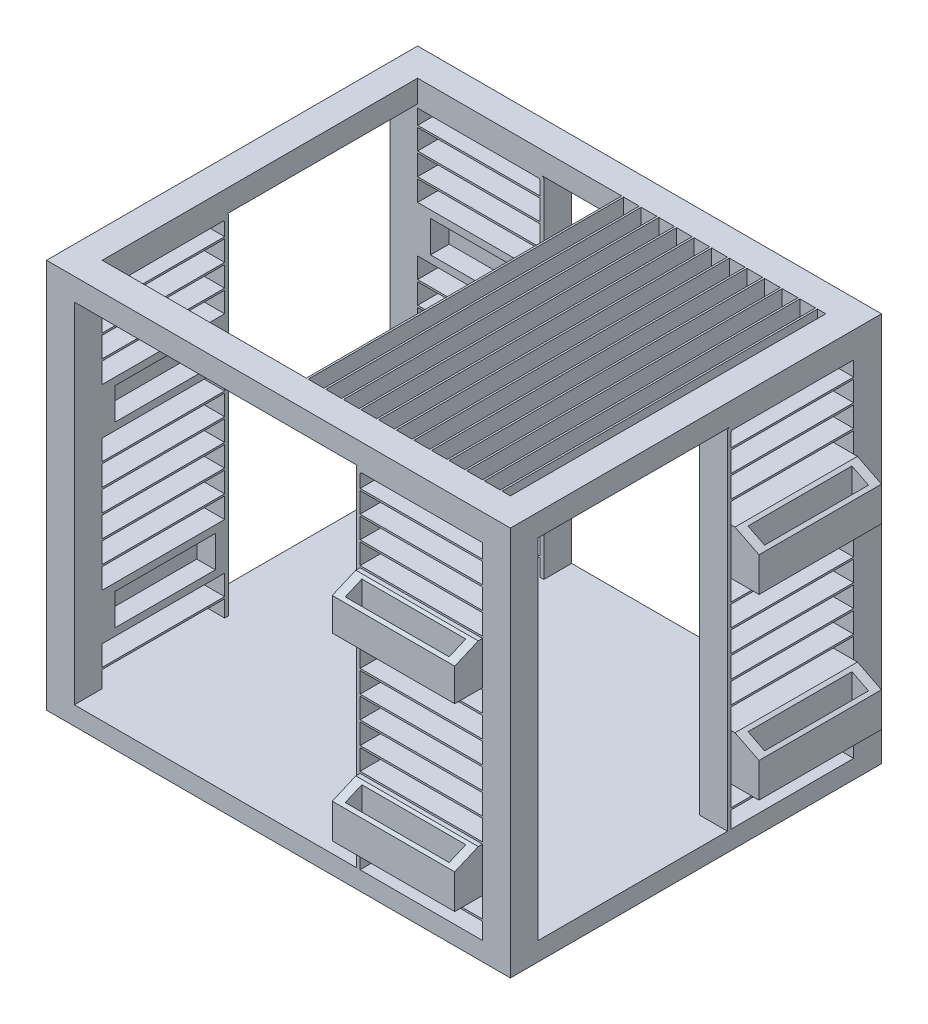
SolidWorks part; units mm, degrees
ref_plane "Front Plane" through (0, 0, 0) normal (0, 0, 1) x (1, 0, 0)
ref_plane "Top Plane" through (0, 0, 0) normal (0, 1, 0) x (1, 0, 0)
ref_plane "Right Plane" through (0, 0, 0) normal (1, 0, 0) x (0, 0, -1)
sketch "Sketch2" plane through (0, 0, 0) normal (0, 1, 0) x (1, 0, 0)
  line L1 (-1250, -1000) -> (1250, -1000)
  line L2 (-1250, -1000) -> (-1250, 1000)
  line L3 (-1250, 1000) -> (1250, 1000)
  line L4 (1250, -1000) -> (1250, 1000)
  line L5 (-1250, -1000) -> (1250, 1000) construction
  line L6 (-1250, 1000) -> (1250, -1000) construction
  point P0 (0, 0)
  dimension "D1" = 2000
  dimension "D2" = 2500
extrude "Boss-Extrude1" add sketch "Sketch2" along normal blind 100
sketch "Sketch3" plane through (0, 100, 0) normal (0, 1, 0) x (1, 0, 0)
  line L1 (-1250, -1000) -> (-1100, -1000)
  line L2 (-1250, -1000) -> (-1250, -850)
  line L3 (-1250, -850) -> (-1100, -850)
  line L4 (-1100, -1000) -> (-1100, -850)
  line L5 (-1250, 1000) -> (-1100, 1000)
  line L6 (-1250, 1000) -> (-1250, 850)
  line L7 (-1250, 850) -> (-1100, 850)
  line L8 (-1100, 1000) -> (-1100, 850)
  line L9 (1250, 1000) -> (1100, 1000)
  line L10 (1250, 1000) -> (1250, 850)
  line L11 (1250, 850) -> (1100, 850)
  line L12 (1100, 1000) -> (1100, 850)
  line L13 (1250, -1000) -> (1100, -1000)
  line L14 (1250, -1000) -> (1250, -850)
  line L15 (1250, -850) -> (1100, -850)
  line L16 (1100, -1000) -> (1100, -850)
  point P20 (0, 0)
  dimension "D1" = 150
extrude "Boss-Extrude3" add sketch "Sketch3" along normal blind 2000
sketch "Sketch6" plane through (0, 100, 0) normal (0, 1, 0) x (1, 0, 0)
  line L0 (-1100, -1000) -> (1100, -1000) construction
  line L1 (420, -850) -> (440, -850)
  line L2 (420, -850) -> (420, -1000)
  line L3 (420, -1000) -> (440, -1000)
  line L4 (440, -850) -> (440, -1000)
  line L5 (1100, -850) -> (1100, -1000) construction
  line L6 (1250, -1000) -> (1250, -850) construction
  line L7 (1100, 1000) -> (-1100, 1000) construction
  line L8 (-440, 1000) -> (-420, 1000)
  line L9 (-440, 1000) -> (-440, 850)
  line L10 (-440, 850) -> (-420, 850)
  line L11 (-420, 1000) -> (-420, 850)
  line L12 (1250, -850) -> (1250, 850) construction
  line L13 (1250, 190) -> (1100, 190)
  line L14 (1250, 190) -> (1250, 170)
  line L15 (1250, 170) -> (1100, 170)
  line L16 (1100, 190) -> (1100, 170)
  line L17 (-1250, 850) -> (-1250, -850) construction
  line L18 (-1250, -170) -> (-1100, -170)
  line L19 (-1250, -170) -> (-1250, -190)
  line L20 (-1250, -190) -> (-1100, -190)
  line L21 (-1100, -170) -> (-1100, -190)
  line L22 (1100, 850) -> (1250, 850) construction
  line L23 (1250, 1000) -> (1100, 1000) construction
  line L25 (-1100, -850) -> (-1250, -850) construction
  line L26 (-1250, -1000) -> (-1100, -1000) construction
  line L27 (-1100, 850) -> (-1100, 1000) construction
  line L28 (-1250, 1000) -> (-1250, 850) construction
  point P10 (420, -925)
  point P31 (1175, 170)
  dimension "D1" = 20
  dimension "D2" = 830
  dimension "D3" = 830
  dimension "D4" = 830
  dimension "D5" = 830
extrude "Boss-Extrude4" add sketch "Sketch6" along normal blind 1880
sketch "Sketch7" plane through (0, 0, 1000) normal (0, 0, 1) x (1, 0, 0)
  line L0 (1100, 2100) -> (1100, 100) construction
  line L1 (420, 1980) -> (1100, 1980)
  line L2 (420, 1980) -> (420, 1956.6642)
  line L3 (420, 1956.6642) -> (1100, 1956.6642)
  line L4 (1100, 1980) -> (1100, 1956.6642)
extrude "Boss-Extrude5" add sketch "Sketch7" against normal blind 150
fillet "Fillet2" radius 10 2 edges at (420, 1980, 925) (440, 1956.6642, 925)
sketch "Sketch8" plane through (1250, 0, 0) normal (1, 0, 0) x (0, 0, -1)
  line L0 (850, 2100) -> (850, 100) construction
  line L1 (170, 1980) -> (850, 1980)
  line L2 (170, 1980) -> (170, 1960)
  line L3 (170, 1960) -> (850, 1960)
  line L4 (850, 1980) -> (850, 1960)
  dimension "D1" = 20
extrude "Boss-Extrude6" add sketch "Sketch8" against normal blind 150
fillet "Fillet3" radius 10 2 edges at (1175, 1980, -170) (1175, 1960, -190)
sketch "Sketch9" plane through (0, 0, -1000) normal (0, 0, -1) x (-1, 0, 0)
  line L0 (1250, 2100) -> (1250, 0) construction
  line L1 (420, 1980) -> (1250, 1980)
  line L2 (420, 1980) -> (420, 1960)
  line L3 (420, 1960) -> (1250, 1960)
  line L4 (1250, 1980) -> (1250, 1960)
  dimension "D1" = 20
extrude "Boss-Extrude7" add sketch "Sketch9" against normal blind 150
fillet "Fillet4" radius 10 2 edges at (-440, 1960, -925) (-420, 1980, -925)
sketch "Sketch10" plane through (-1250, 0, 0) normal (-1, 0, 0) x (0, 0, 1)
  line L5 (170, 1980) -> (1000, 1980)
  line L6 (170, 1980) -> (170, 1956.6642)
  line L7 (170, 1956.6642) -> (1000, 1956.6642)
  line L8 (1000, 1980) -> (1000, 1956.6642)
extrude "Boss-Extrude8" add sketch "Sketch10" against normal blind 150
fillet "Fillet5" radius 10 2 edges at (-1175, 1980, 170) (-1175, 1956.6642, 190)
sketch "Sketch11" plane through (0, 2100, 0) normal (0, 1, 0) x (1, 0, 0)
  line L0 (-1100, -1000) -> (-1100, -850) construction
  line L1 (1100, -850) -> (-1100, -850)
  line L2 (1100, -850) -> (1100, -1000)
  line L4 (-1100, -850) -> (-1100, -1000)
  line L5 (-1100, -1000) -> (-1100, -850) construction
  line L7 (-1250, 850) -> (-1100, 850)
  line L8 (-1250, 850) -> (-1250, -850)
  line L9 (-1250, -850) -> (-1100, -850)
  line L10 (-1100, 850) -> (-1100, -850)
  line L11 (-1100, 1000) -> (1100, 1000)
  line L12 (-1100, 1000) -> (-1100, 850)
  line L13 (-1100, 850) -> (1100, 850)
  line L14 (1100, 1000) -> (1100, 850)
  line L15 (1250, 850) -> (1100, 850)
  line L16 (1250, 850) -> (1250, -850)
  line L17 (1250, -850) -> (1100, -850)
  line L18 (1100, 850) -> (1100, -850)
  line L19 (-1100, -850) -> (1100, -850)
  line L20 (-1100, -850) -> (-1100, -1000)
  line L21 (-1100, -1000) -> (1100, -1000)
  line L22 (1100, -850) -> (1100, -1000)
  line M2 (1250, -850) -> (1100, -850)
  line M3 (1100, -850) -> (1100, -1000)
extrude "Boss-Extrude11" add sketch "Sketch11" against normal blind 120 contours L10 L7 L8 L9 | L4 L21 L1 M3 | L15 L18 L16 M2 | L14 L11 L12 L13
sketch "Sketch12" plane through (0, 0, 190) normal (0, 0, 1) x (1, 0, 0)
  line L0 (-1250, 2100) -> (-1250, 0) construction
  line L1 (-1250, 1880) -> (-1100, 1880)
  line L2 (-1250, 1880) -> (-1250, 1870)
  line L3 (-1250, 1870) -> (-1100, 1870)
  line L4 (-1100, 1880) -> (-1100, 1870)
  line L5 (-1100, 1980) -> (-1100, 100) construction
  line L6 (-1250, 1760) -> (-1250, 1750)
  line L7 (-1250, 1760) -> (-1100, 1760)
  line L8 (-1100, 1760) -> (-1100, 1750)
  line L9 (-1250, 1750) -> (-1100, 1750)
  line L10 (-1250, 1640) -> (-1250, 1630)
  line L11 (-1250, 1640) -> (-1100, 1640)
  line L12 (-1100, 1640) -> (-1100, 1630)
  line L13 (-1250, 1630) -> (-1100, 1630)
  line L14 (-1250, 1520) -> (-1250, 1510)
  line L15 (-1250, 1520) -> (-1100, 1520)
  line L16 (-1100, 1520) -> (-1100, 1510)
  line L17 (-1250, 1510) -> (-1100, 1510)
  line L18 (-1250, 1400) -> (-1250, 1390)
  line L19 (-1250, 1400) -> (-1100, 1400)
  line L20 (-1100, 1400) -> (-1100, 1390)
  line L21 (-1250, 1390) -> (-1100, 1390)
  line L22 (-1250, 1280) -> (-1250, 1270)
  line L23 (-1250, 1280) -> (-1100, 1280)
  line L24 (-1100, 1280) -> (-1100, 1270)
  line L25 (-1250, 1270) -> (-1100, 1270)
  line L26 (-1250, 1160) -> (-1250, 1150)
  line L27 (-1250, 1160) -> (-1100, 1160)
  line L28 (-1100, 1160) -> (-1100, 1150)
  line L29 (-1250, 1150) -> (-1100, 1150)
  line L30 (-1250, 1040) -> (-1250, 1030)
  line L31 (-1250, 1040) -> (-1100, 1040)
  line L32 (-1100, 1040) -> (-1100, 1030)
  line L33 (-1250, 1030) -> (-1100, 1030)
  line L34 (-1250, 920) -> (-1250, 910)
  line L35 (-1250, 920) -> (-1100, 920)
  line L36 (-1100, 920) -> (-1100, 910)
  line L37 (-1250, 910) -> (-1100, 910)
  line L38 (-1250, 800) -> (-1250, 790)
  line L39 (-1250, 800) -> (-1100, 800)
  line L40 (-1100, 800) -> (-1100, 790)
  line L41 (-1250, 790) -> (-1100, 790)
  line L42 (-1250, 680) -> (-1250, 670)
  line L43 (-1250, 680) -> (-1100, 680)
  line L44 (-1100, 680) -> (-1100, 670)
  line L45 (-1250, 670) -> (-1100, 670)
  line L46 (-1250, 560) -> (-1250, 550)
  line L47 (-1250, 560) -> (-1100, 560)
  line L48 (-1100, 560) -> (-1100, 550)
  line L49 (-1250, 550) -> (-1100, 550)
  line L50 (-1250, 440) -> (-1250, 430)
  line L51 (-1250, 440) -> (-1100, 440)
  line L52 (-1100, 440) -> (-1100, 430)
  line L53 (-1250, 430) -> (-1100, 430)
  line L54 (-1250, 320) -> (-1250, 310)
  line L55 (-1250, 320) -> (-1100, 320)
  line L56 (-1100, 320) -> (-1100, 310)
  line L57 (-1250, 310) -> (-1100, 310)
  line L58 (-1250, 200) -> (-1250, 190)
  line L59 (-1250, 200) -> (-1100, 200)
  line L60 (-1100, 200) -> (-1100, 190)
  line L61 (-1250, 190) -> (-1100, 190)
  line L62 (-1100, 1980) -> (430, 1980) construction
  point P66 (-1175, 1880)
  dimension "D2" = 10
  dimension "D3" = 100
  dimension "D1" = 15
extrude "Boss-Extrude12" add sketch "Sketch12" along normal up to surface (660 mm away) up to face at (-1175, 1028.3321, 850)
sketch "Sketch14" plane through (440, 0, 0) normal (1, 0, 0) x (0, 0, -1)
  line L0 (-1000, 2100) -> (-1000, 0) construction
  line L1 (-850, 1880) -> (-1000, 1880)
  line L2 (-850, 1880) -> (-850, 1870)
  line L3 (-850, 1870) -> (-1000, 1870)
  line L4 (-1000, 1880) -> (-1000, 1870)
  line L5 (-850, 1760) -> (-1000, 1760)
  line L6 (-850, 1760) -> (-850, 1750)
  line L7 (-850, 1750) -> (-1000, 1750)
  line L8 (-1000, 1760) -> (-1000, 1750)
  line L9 (-850, 1640) -> (-1000, 1640)
  line L10 (-850, 1640) -> (-850, 1630)
  line L11 (-850, 1630) -> (-1000, 1630)
  line L12 (-1000, 1640) -> (-1000, 1630)
  line L13 (-850, 1520) -> (-1000, 1520)
  line L14 (-850, 1520) -> (-850, 1510)
  line L15 (-850, 1510) -> (-1000, 1510)
  line L16 (-1000, 1520) -> (-1000, 1510)
  line L17 (-850, 1400) -> (-1000, 1400)
  line L18 (-850, 1400) -> (-850, 1390)
  line L19 (-850, 1390) -> (-1000, 1390)
  line L20 (-1000, 1400) -> (-1000, 1390)
  line L21 (-850, 1280) -> (-1000, 1280)
  line L22 (-850, 1280) -> (-850, 1270)
  line L23 (-850, 1270) -> (-1000, 1270)
  line L24 (-1000, 1280) -> (-1000, 1270)
  line L25 (-850, 1160) -> (-1000, 1160)
  line L26 (-850, 1160) -> (-850, 1150)
  line L27 (-850, 1150) -> (-1000, 1150)
  line L28 (-1000, 1160) -> (-1000, 1150)
  line L29 (-850, 1040) -> (-1000, 1040)
  line L30 (-850, 1040) -> (-850, 1030)
  line L31 (-850, 1030) -> (-1000, 1030)
  line L32 (-1000, 1040) -> (-1000, 1030)
  line L33 (-850, 920) -> (-1000, 920)
  line L34 (-850, 920) -> (-850, 910)
  line L35 (-850, 910) -> (-1000, 910)
  line L36 (-1000, 920) -> (-1000, 910)
  line L37 (-850, 800) -> (-1000, 800)
  line L38 (-850, 800) -> (-850, 790)
  line L39 (-850, 790) -> (-1000, 790)
  line L40 (-1000, 800) -> (-1000, 790)
  line L41 (-850, 680) -> (-1000, 680)
  line L42 (-850, 680) -> (-850, 670)
  line L43 (-850, 670) -> (-1000, 670)
  line L44 (-1000, 680) -> (-1000, 670)
  line L45 (-850, 560) -> (-1000, 560)
  line L46 (-850, 560) -> (-850, 550)
  line L47 (-850, 550) -> (-1000, 550)
  line L48 (-1000, 560) -> (-1000, 550)
  line L49 (-850, 440) -> (-1000, 440)
  line L50 (-850, 440) -> (-850, 430)
  line L51 (-850, 430) -> (-1000, 430)
  line L52 (-1000, 440) -> (-1000, 430)
  line L53 (-850, 320) -> (-1000, 320)
  line L54 (-850, 320) -> (-850, 310)
  line L55 (-850, 310) -> (-1000, 310)
  line L56 (-1000, 320) -> (-1000, 310)
  line L57 (-850, 200) -> (-1000, 200)
  line L58 (-850, 200) -> (-850, 190)
  line L59 (-850, 190) -> (-1000, 190)
  line L60 (-1000, 200) -> (-1000, 190)
  dimension "D1" = 10
  dimension "D2" = 15
extrude "Boss-Extrude13" add sketch "Sketch14" along normal up to surface (660 mm away) up to face at (1100, 1028.3321, 925)
sketch "Sketch15" plane through (0, 0, -190) normal (0, 0, -1) x (-1, 0, 0)
  line L0 (-1250, 2100) -> (-1250, 0) construction
  line L1 (-1100, 1880) -> (-1250, 1880)
  line L2 (-1100, 1880) -> (-1100, 1870)
  line L3 (-1100, 1870) -> (-1250, 1870)
  line L4 (-1250, 1880) -> (-1250, 1870)
  line L5 (-1100, 1760) -> (-1250, 1760)
  line L6 (-1100, 1750) -> (-1250, 1750)
  line L7 (-1100, 1760) -> (-1100, 1750)
  line L8 (-1250, 1760) -> (-1250, 1750)
  line L9 (-1100, 1640) -> (-1250, 1640)
  line L10 (-1100, 1630) -> (-1250, 1630)
  line L11 (-1100, 1640) -> (-1100, 1630)
  line L12 (-1250, 1640) -> (-1250, 1630)
  line L13 (-1100, 1520) -> (-1250, 1520)
  line L14 (-1100, 1510) -> (-1250, 1510)
  line L15 (-1100, 1520) -> (-1100, 1510)
  line L16 (-1250, 1520) -> (-1250, 1510)
  line L17 (-1100, 1400) -> (-1250, 1400)
  line L18 (-1100, 1390) -> (-1250, 1390)
  line L19 (-1100, 1400) -> (-1100, 1390)
  line L20 (-1250, 1400) -> (-1250, 1390)
  line L21 (-1100, 1280) -> (-1250, 1280)
  line L22 (-1100, 1270) -> (-1250, 1270)
  line L23 (-1100, 1280) -> (-1100, 1270)
  line L24 (-1250, 1280) -> (-1250, 1270)
  line L25 (-1100, 1160) -> (-1250, 1160)
  line L26 (-1100, 1150) -> (-1250, 1150)
  line L27 (-1100, 1160) -> (-1100, 1150)
  line L28 (-1250, 1160) -> (-1250, 1150)
  line L29 (-1100, 1040) -> (-1250, 1040)
  line L30 (-1100, 1030) -> (-1250, 1030)
  line L31 (-1100, 1040) -> (-1100, 1030)
  line L32 (-1250, 1040) -> (-1250, 1030)
  line L33 (-1100, 920) -> (-1250, 920)
  line L34 (-1100, 910) -> (-1250, 910)
  line L35 (-1100, 920) -> (-1100, 910)
  line L36 (-1250, 920) -> (-1250, 910)
  line L37 (-1100, 800) -> (-1250, 800)
  line L38 (-1100, 790) -> (-1250, 790)
  line L39 (-1100, 800) -> (-1100, 790)
  line L40 (-1250, 800) -> (-1250, 790)
  line L41 (-1100, 680) -> (-1250, 680)
  line L42 (-1100, 670) -> (-1250, 670)
  line L43 (-1100, 680) -> (-1100, 670)
  line L44 (-1250, 680) -> (-1250, 670)
  line L45 (-1100, 560) -> (-1250, 560)
  line L46 (-1100, 550) -> (-1250, 550)
  line L47 (-1100, 560) -> (-1100, 550)
  line L48 (-1250, 560) -> (-1250, 550)
  line L49 (-1100, 440) -> (-1250, 440)
  line L50 (-1100, 430) -> (-1250, 430)
  line L51 (-1100, 440) -> (-1100, 430)
  line L52 (-1250, 440) -> (-1250, 430)
  line L53 (-1100, 320) -> (-1250, 320)
  line L54 (-1100, 310) -> (-1250, 310)
  line L55 (-1100, 320) -> (-1100, 310)
  line L56 (-1250, 320) -> (-1250, 310)
  line L57 (-1100, 200) -> (-1250, 200)
  line L58 (-1100, 190) -> (-1250, 190)
  line L59 (-1100, 200) -> (-1100, 190)
  line L60 (-1250, 200) -> (-1250, 190)
  dimension "D1" = 10
  dimension "D2" = 15
extrude "Boss-Extrude14" add sketch "Sketch15" along normal up to surface (660 mm away) up to face at (1175, 1030, -850)
sketch "Sketch16" plane through (-440, 0, 0) normal (-1, 0, 0) x (0, 0, 1)
  line L0 (-1000, 2100) -> (-1000, 0) construction
  line L1 (-850, 1880) -> (-1000, 1880)
  line L2 (-850, 1880) -> (-850, 1870)
  line L3 (-850, 1870) -> (-1000, 1870)
  line L4 (-1000, 1880) -> (-1000, 1870)
  line L5 (-850, 1760) -> (-1000, 1760)
  line L6 (-850, 1750) -> (-1000, 1750)
  line L7 (-850, 1760) -> (-850, 1750)
  line L8 (-1000, 1760) -> (-1000, 1750)
  line L9 (-850, 1640) -> (-1000, 1640)
  line L10 (-850, 1630) -> (-1000, 1630)
  line L11 (-850, 1640) -> (-850, 1630)
  line L12 (-1000, 1640) -> (-1000, 1630)
  line L13 (-850, 1520) -> (-1000, 1520)
  line L14 (-850, 1510) -> (-1000, 1510)
  line L15 (-850, 1520) -> (-850, 1510)
  line L16 (-1000, 1520) -> (-1000, 1510)
  line L17 (-850, 1400) -> (-1000, 1400)
  line L18 (-850, 1390) -> (-1000, 1390)
  line L19 (-850, 1400) -> (-850, 1390)
  line L20 (-1000, 1400) -> (-1000, 1390)
  line L21 (-850, 1280) -> (-1000, 1280)
  line L22 (-850, 1270) -> (-1000, 1270)
  line L23 (-850, 1280) -> (-850, 1270)
  line L24 (-1000, 1280) -> (-1000, 1270)
  line L25 (-850, 1160) -> (-1000, 1160)
  line L26 (-850, 1150) -> (-1000, 1150)
  line L27 (-850, 1160) -> (-850, 1150)
  line L28 (-1000, 1160) -> (-1000, 1150)
  line L29 (-850, 1040) -> (-1000, 1040)
  line L30 (-850, 1030) -> (-1000, 1030)
  line L31 (-850, 1040) -> (-850, 1030)
  line L32 (-1000, 1040) -> (-1000, 1030)
  line L33 (-850, 920) -> (-1000, 920)
  line L34 (-850, 910) -> (-1000, 910)
  line L35 (-850, 920) -> (-850, 910)
  line L36 (-1000, 920) -> (-1000, 910)
  line L37 (-850, 800) -> (-1000, 800)
  line L38 (-850, 790) -> (-1000, 790)
  line L39 (-850, 800) -> (-850, 790)
  line L40 (-1000, 800) -> (-1000, 790)
  line L41 (-850, 680) -> (-1000, 680)
  line L42 (-850, 670) -> (-1000, 670)
  line L43 (-850, 680) -> (-850, 670)
  line L44 (-1000, 680) -> (-1000, 670)
  line L45 (-850, 560) -> (-1000, 560)
  line L46 (-850, 550) -> (-1000, 550)
  line L47 (-850, 560) -> (-850, 550)
  line L48 (-1000, 560) -> (-1000, 550)
  line L49 (-850, 440) -> (-1000, 440)
  line L50 (-850, 430) -> (-1000, 430)
  line L51 (-850, 440) -> (-850, 430)
  line L52 (-1000, 440) -> (-1000, 430)
  line L53 (-850, 320) -> (-1000, 320)
  line L54 (-850, 310) -> (-1000, 310)
  line L55 (-850, 320) -> (-850, 310)
  line L56 (-1000, 320) -> (-1000, 310)
  line L57 (-850, 200) -> (-1000, 200)
  line L58 (-850, 190) -> (-1000, 190)
  line L59 (-850, 200) -> (-850, 190)
  line L60 (-1000, 200) -> (-1000, 190)
  line L61 (-850, 1880) -> (-850, 1760) construction
  dimension "D1" = 10
  dimension "D3" = 120
  dimension "D2" = 15
extrude "Boss-Extrude15" add sketch "Sketch16" along normal up to surface (660 mm away) up to face at (-1100, 1030, -925)
sketch "Sketch17" plane through (-1250, 0, 0) normal (-1, 0, 0) x (0, 0, 1)
  line L1 (190, 560) -> (850, 560)
  line L2 (190, 560) -> (190, 310)
  line L3 (190, 310) -> (850, 310)
  line L4 (850, 560) -> (850, 310)
  line L5 (190, 1520) -> (850, 1520)
  line L6 (190, 1520) -> (190, 1270)
  line L7 (190, 1270) -> (850, 1270)
  line L8 (850, 1520) -> (850, 1270)
extrude "Boss-Extrude21" add sketch "Sketch17" along normal mid plane 300
sketch "Sketch18" plane through (0, 0, 1000) normal (0, 0, 1) x (1, 0, 0)
  line L1 (440, 1510) -> (1100, 1510)
  line L2 (440, 1510) -> (440, 1280)
  line L3 (440, 1280) -> (1100, 1280)
  line L4 (1100, 1510) -> (1100, 1280)
  line L5 (440, 550) -> (1100, 550)
  line L6 (440, 550) -> (440, 310)
  line L7 (440, 310) -> (1100, 310)
  line L8 (1100, 550) -> (1100, 310)
extrude "Boss-Extrude23" add sketch "Sketch18" along normal mid plane 300
sketch "Sketch19" plane through (1250, 0, 0) normal (1, 0, 0) x (0, 0, -1)
  line L1 (190, 1520) -> (850, 1520)
  line L2 (190, 1520) -> (190, 1270)
  line L3 (190, 1270) -> (850, 1270)
  line L4 (850, 1520) -> (850, 1270)
  line L6 (190, 560) -> (850, 560)
  line L7 (190, 560) -> (190, 310)
  line L8 (190, 310) -> (850, 310)
  line L9 (850, 560) -> (850, 310)
extrude "Boss-Extrude24" add sketch "Sketch19" along normal mid plane 300
sketch "Sketch20" plane through (0, 0, -1000) normal (0, 0, -1) x (-1, 0, 0)
  line L1 (440, 1520) -> (1100, 1520)
  line L2 (440, 1520) -> (440, 1270)
  line L3 (440, 1270) -> (1100, 1270)
  line L4 (1100, 1520) -> (1100, 1270)
  line L5 (440, 560) -> (1100, 560)
  line L6 (440, 560) -> (440, 310)
  line L7 (440, 310) -> (1100, 310)
  line L8 (1100, 560) -> (1100, 310)
extrude "Boss-Extrude25" add sketch "Sketch20" along normal mid plane 300
sketch "Sketch22" plane through (-1100, 0, 0) normal (1, 0, 0) x (0, 0, -1)
  line L0 (850, 1520) -> (190, 1520) construction
  line L1 (850, 560) -> (190, 560) construction
  line L2 (850, 1980) -> (850, 100) construction
  line L3 (783.9264, 1480) -> (256.0557, 1480)
  line L4 (783.9264, 1480) -> (783.9264, 1310)
  line L5 (783.9264, 1310) -> (256.0557, 1310)
  line L6 (256.0557, 1480) -> (256.0557, 1310)
  line L7 (783.9264, 1480) -> (256.0557, 1310) construction
  line L8 (783.9264, 1310) -> (256.0557, 1480) construction
  line L9 (780, 520) -> (252.1293, 520)
  line L10 (780, 520) -> (780, 350)
  line L11 (780, 350) -> (252.1293, 350)
  line L12 (252.1293, 520) -> (252.1293, 350)
  point P2 (519.9911, 1395)
  dimension "D1" = 170
  dimension "D2" = 527.8707
  dimension "D3" = 40
  dimension "D4" = 66.0736
  dimension "D5" = 70
  dimension "D6" = 40
extrude "Cut-Extrude2" cut sketch "Sketch22" along normal blind 2300
sketch "Sketch23" plane through (0, 0, -850) normal (0, 0, 1) x (1, 0, 0)
  line L0 (-1100, 1520) -> (-440, 1520) construction
  line L1 (-1030, 1480) -> (-490, 1480)
  line L2 (-1030, 1480) -> (-1030, 1310)
  line L3 (-1030, 1310) -> (-490, 1310)
  line L4 (-490, 1480) -> (-490, 1310)
  line L5 (-1030, 520) -> (-490, 520)
  line L6 (-1030, 520) -> (-1030, 350)
  line L7 (-1030, 350) -> (-490, 350)
  line L8 (-490, 520) -> (-490, 350)
  line L9 (-1100, 1980) -> (-1100, 100) construction
  line L10 (-1100, 560) -> (-440, 560) construction
  point P10 (-1030, 1395)
  point P13 (0, 0)
  dimension "D1" = 170
  dimension "D2" = 540
  dimension "D3" = 40
  dimension "D4" = 70
  dimension "D5" = 40
extrude "Cut-Extrude3" cut sketch "Sketch23" against normal blind 100
sketch "Sketch24" plane through (-1100, 0, 0) normal (1, 0, 0) x (0, 0, -1)
  line L0 (-850, 1520) -> (-190, 1520) construction
  line L1 (-780, 1480) -> (-240, 1480)
  line L2 (-780, 1480) -> (-780, 1310)
  line L3 (-780, 1310) -> (-240, 1310)
  line L4 (-240, 1480) -> (-240, 1310)
  line L5 (-780, 520) -> (-240, 520)
  line L6 (-780, 520) -> (-780, 350)
  line L7 (-780, 350) -> (-240, 350)
  line L8 (-240, 520) -> (-240, 350)
  line L9 (-850, 1980) -> (-850, 100) construction
  line L10 (-850, 560) -> (-190, 560) construction
  point P8 (0, 0)
  dimension "D1" = 170
  dimension "D2" = 540
  dimension "D3" = 40
  dimension "D4" = 70
  dimension "D5" = 40
extrude "Cut-Extrude4" cut sketch "Sketch24" against normal blind 100
sketch "Sketch25" plane through (0, 0, 850) normal (0, 0, -1) x (-1, 0, 0)
  line L0 (-1100, 560) -> (-440, 560) construction
  line L1 (-1030, 1480) -> (-490, 1480)
  line L2 (-1030, 1480) -> (-1030, 1310)
  line L3 (-1030, 1310) -> (-490, 1310)
  line L4 (-490, 1480) -> (-490, 1310)
  line L5 (-1030, 520) -> (-490, 520)
  line L6 (-1030, 520) -> (-1030, 350)
  line L7 (-1030, 350) -> (-490, 350)
  line L8 (-490, 520) -> (-490, 350)
  line L9 (-1100, 1520) -> (-440, 1520) construction
  line L10 (-1100, 1980) -> (-1100, 100) construction
  point P8 (0, 0)
  dimension "D1" = 40
  dimension "D2" = 40
  dimension "D3" = 170
  dimension "D4" = 540
  dimension "D5" = 70
extrude "Cut-Extrude5" cut sketch "Sketch25" against normal blind 100
sketch "Sketch26" plane through (0, 0, 1000) normal (0, 0, 1) x (1, 0, 0)
  line L5 (0, 2100) -> (0, -216.6032) construction
  line L6 (-1250, 2100) -> (1250, 2100) construction
  line L7 (-1270.541, 1520) -> (-1400, 1455.3264)
  line L8 (-1400, 1520) -> (-1250, 1520) construction
  line L9 (-1400, 1270) -> (-1400, 1520) construction
  line L10 (-1400, 1455.3264) -> (-1400, 1520)
  line L11 (-1400, 1520) -> (-1270.541, 1520)
  line L12 (-1270.541, 560) -> (-1400, 495.3264)
  line L13 (-1400, 560) -> (-1250, 560) construction
  line L14 (-1400, 310) -> (-1400, 560) construction
  line L15 (-1400, 495.3264) -> (-1400, 560)
  line L16 (-1400, 560) -> (-1270.541, 560)
  line L17 (1400, 1455.3264) -> (1400, 1520)
  line L18 (1400, 495.3264) -> (1400, 560)
  line L19 (1400, 560) -> (1270.541, 560)
  line L20 (1270.541, 560) -> (1400, 495.3264)
  line L21 (1400, 1520) -> (1270.541, 1520)
  line L22 (1270.541, 1520) -> (1400, 1455.3264)
extrude "Cut-Extrude8" cut sketch "Sketch26" against normal through all
sketch "Sketch29" plane through (1250, 0, 0) normal (1, 0, 0) x (0, 0, -1)
  line L0 (1150, 1455.3264) -> (1000, 1520)
  line L1 (1150, 1520) -> (1150, 1270) construction
  line L2 (1000, 1520) -> (1150, 1520)
  line L3 (1150, 1520) -> (1150, 1455.3264)
  line L4 (1000, 560) -> (1150, 495.3264)
  line L7 (1150, 560) -> (1150, 310) construction
  line L8 (1150, 560) -> (1150, 495.3264)
  line L9 (1150, 560) -> (1000, 560)
  line L10 (0, 0) -> (0, 1166.0247) construction
  line L11 (-1000, 560) -> (-1150, 495.3264)
  line L12 (-1150, 560) -> (-1150, 495.3264)
  line L13 (-1150, 560) -> (-1000, 560)
  line L14 (-1150, 1520) -> (-1150, 1455.3264)
  line L15 (-1150, 1455.3264) -> (-1000, 1520)
  line L16 (-1000, 1520) -> (-1150, 1520)
extrude "Cut-Extrude9" cut sketch "Sketch29" against normal through all
sketch "Sketch30" plane through (0, 2100, 0) normal (0, 1, 0) x (1, 0, 0)
  line L0 (-1400, -190) -> (-1270.541, -190) construction
  line L1 (-1380, -240) -> (-1290.541, -240)
  line L2 (-1380, -240) -> (-1380, -800)
  line L3 (-1380, -800) -> (-1290.541, -800)
  line L4 (-1290.541, -240) -> (-1290.541, -800)
  line L5 (490, -1040.541) -> (1050, -1040.541)
  line L6 (490, -1040.541) -> (490, -1130)
  line L7 (490, -1130) -> (1050, -1130)
  line L8 (1050, -1040.541) -> (1050, -1130)
  line L9 (1290.541, 800) -> (1380, 800)
  line L10 (1290.541, 800) -> (1290.541, 240)
  line L11 (1290.541, 240) -> (1380, 240)
  line L12 (1380, 800) -> (1380, 240)
  line L13 (-1050, 1130) -> (-490, 1130)
  line L14 (-1050, 1130) -> (-1050, 1040.541)
  line L15 (-1050, 1040.541) -> (-490, 1040.541)
  line L16 (-490, 1130) -> (-490, 1040.541)
  line L17 (-1270.541, -850) -> (-1400, -850) construction
  line L18 (-1400, -190) -> (-1400, -850) construction
  line L19 (-1270.541, -190) -> (-1270.541, -850) construction
  line L20 (-440, 1150) -> (-440, 1000) construction
  line L22 (1400, 190) -> (1270.541, 190) construction
  line L23 (1400, 190) -> (1400, 850) construction
  line L24 (440, -1150) -> (440, -1023.1934) construction
  line L25 (440, -1150) -> (1100, -1150) construction
  line L26 (-440, 1150) -> (-1100, 1150) construction
  point P18 (-1335.2705, -190)
  point P21 (-1380, -520)
  point P26 (-490, 1085.2705)
  point P33 (1400, 520)
  point P34 (490, -1085.2705)
  point P41 (0, 0)
  dimension "D1" = 50
  dimension "D2" = 50
  dimension "D3" = 20
  dimension "D4" = 20
  dimension "D5" = 50
  dimension "D6" = 50
  dimension "D7" = 20
  dimension "D8" = 50
  dimension "D9" = 20
  dimension "D10" = 20
extrude "Cut-Extrude10" cut sketch "Sketch30" against normal blind 800
ref_plane "Plane7" through (0, 1040, 0) normal (0, 1, 0) x (1, 0, 0)
mirror "Mirror10" about plane through (0, 1040, 0) normal (0, 1, 0) of "Cut-Extrude10"
sketch "Sketch31" plane through (0, 310, 0) normal (0, -1, 0) x (1, 0, 0)
  line L0 (1290.541, -240) -> (1290.541, -800) construction
  line L1 (1050, 1130) -> (490, 1130)
  line L2 (1050, 1130) -> (1050, 1040.541)
  line L3 (1050, 1040.541) -> (490, 1040.541)
  line L4 (490, 1130) -> (490, 1040.541)
  line L5 (1380, -240) -> (1290.541, -240)
  line L6 (1380, -240) -> (1380, -800)
  line L7 (1380, -800) -> (1290.541, -800)
  line L8 (1290.541, -240) -> (1290.541, -800)
  line L9 (-1380, 240) -> (-1290.541, 240) construction
  line L10 (-490, -1040.541) -> (-1050, -1040.541)
  line L11 (-490, -1040.541) -> (-490, -1130)
  line L12 (-490, -1130) -> (-1050, -1130)
  line L13 (-1050, -1040.541) -> (-1050, -1130)
  line L14 (-1290.541, 800) -> (-1380, 800)
  line L15 (-1290.541, 800) -> (-1290.541, 240)
  line L16 (-1290.541, 240) -> (-1380, 240)
  line L17 (-1380, 800) -> (-1380, 240)
  line L18 (-1380, 800) -> (-1380, 240) construction
extrude "Boss-Extrude26" add sketch "Sketch31" against normal blind 30
sketch "Sketch33" plane through (0, 0, -850) normal (0, 0, 1) x (1, 0, 0)
  line L1 (-1250, 2100) -> (1250, 2100) construction
  line L2 (-1100, 1980) -> (430, 1980) construction
  line L3 (0, 2100) -> (10, 2100)
  line L4 (0, 2100) -> (0, 1980)
  line L5 (0, 1980) -> (10, 1980)
  line L6 (10, 2100) -> (10, 1980)
  line L11 (105, 2100) -> (105, 1980)
  line L12 (95, 2100) -> (95, 1980)
  line L13 (95, 2100) -> (105, 2100)
  line L14 (95, 1980) -> (105, 1980)
  line L15 (200, 2100) -> (200, 1980)
  line L16 (190, 2100) -> (190, 1980)
  line L17 (190, 2100) -> (200, 2100)
  line L18 (190, 1980) -> (200, 1980)
  line L19 (295, 2100) -> (295, 1980)
  line L20 (285, 2100) -> (285, 1980)
  line L21 (285, 2100) -> (295, 2100)
  line L22 (285, 1980) -> (295, 1980)
  line L23 (390, 2100) -> (390, 1980)
  line L24 (380, 2100) -> (380, 1980)
  line L25 (380, 2100) -> (390, 2100)
  line L26 (380, 1980) -> (390, 1980)
  line L27 (485, 2100) -> (485, 1980)
  line L28 (475, 2100) -> (475, 1980)
  line L29 (475, 2100) -> (485, 2100)
  line L30 (475, 1980) -> (485, 1980)
  line L31 (580, 2100) -> (580, 1980)
  line L32 (570, 2100) -> (570, 1980)
  line L33 (570, 2100) -> (580, 2100)
  line L34 (570, 1980) -> (580, 1980)
  line L35 (675, 2100) -> (675, 1980)
  line L36 (665, 2100) -> (665, 1980)
  line L37 (665, 2100) -> (675, 2100)
  line L38 (665, 1980) -> (675, 1980)
  line L39 (770, 2100) -> (770, 1980)
  line L40 (760, 2100) -> (760, 1980)
  line L41 (760, 2100) -> (770, 2100)
  line L42 (760, 1980) -> (770, 1980)
  line L43 (865, 2100) -> (865, 1980)
  line L44 (855, 2100) -> (855, 1980)
  line L45 (855, 2100) -> (865, 2100)
  line L46 (855, 1980) -> (865, 1980)
  line L47 (960, 2100) -> (960, 1980)
  line L48 (950, 2100) -> (950, 1980)
  line L49 (950, 2100) -> (960, 2100)
  line L50 (950, 1980) -> (960, 1980)
  line L51 (1055, 2100) -> (1055, 1980)
  line L52 (1045, 2100) -> (1045, 1980)
  line L53 (1045, 2100) -> (1055, 2100)
  line L54 (1045, 1980) -> (1055, 1980)
  dimension "D1" = 10
  dimension "D2" = 12
extrude "Boss-Extrude27" add sketch "Sketch33" along normal up to surface (1700 mm away) up to face at (760, 1395, 850)
